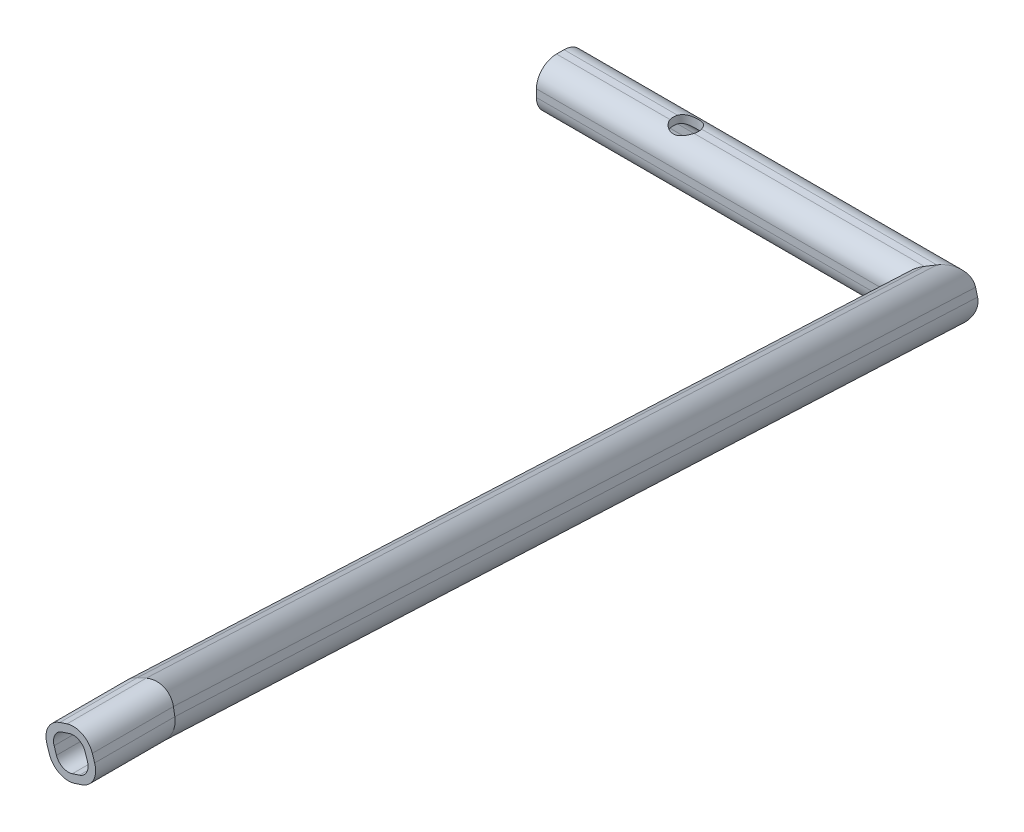
SolidWorks part; units mm, degrees
material "5052-H38, Rod (SS)"
ref_plane "Front Plane" through (0, 0, 0) normal (0, 0, 1) x (1, 0, 0)
ref_plane "Top Plane" through (0, 0, 0) normal (0, 1, 0) x (1, 0, 0)
ref_plane "Right Plane" through (0, 0, 0) normal (1, 0, 0) x (0, 0, -1)
sketch "Sketch2" plane through (0, 0, 0) normal (1, 0, 0) x (0, 0, -1)
  line L1 (-1.5, -6.5) -> (1.5, -6.5)
  line L2 (-6.5, -1.5) -> (-6.5, 1.5)
  line L3 (-1.5, 6.5) -> (1.5, 6.5)
  line L4 (6.5, -1.5) -> (6.5, 1.5)
  line L5 (-6.5, -6.5) -> (6.5, 6.5) construction
  line L6 (-6.5, 6.5) -> (6.5, -6.5) construction
  arc A0 (6.5, -1.5) -> (1.5, -6.5) centre (1.5, -1.5) cw
  arc A1 (-1.5, -6.5) -> (-6.5, -1.5) centre (-1.5, -1.5) cw
  arc A2 (-6.5, 1.5) -> (-1.5, 6.5) centre (-1.5, 1.5) cw
  arc A3 (1.5, 6.5) -> (6.5, 1.5) centre (1.5, 1.5) cw
  point P0 (0, 0)
  dimension "D3" = 5
  dimension "D1" = 13
  dimension "D2" = 13
sketch3d "3DSketch2"
  line L0 (0, 0, 0) -> (335.0752, 0, 0) construction
  line L1 (335.0752, 0, 0) -> (335.0752, 200, 0) construction
  line L2 (335.0752, 200, 0) -> (335.0752, 200, 500) construction
  line L3 (0, 0, 0) -> (150, 0, 0)
  line L4 (150, 0, 0) -> (335.0752, 200, 500)
  line L5 (335.0752, 200, 500) -> (335.0752, 200, 530)
  line L6 (0, 0, 0) -> (0, -210, 0) construction
  dimension "D1" = 150
  dimension "D2" = 30
  dimension "D3" = 200
  dimension "D4" = 500
  dimension "D5" = 210
sweep "Sweep-Thin3" add profiles "Sketch2" path "3DSketch2" parameters "D1"=3
sketch "Sketch21" plane through (0, 0, 0) normal (0, 1, 0) x (1, 0, 0)
  line L0 (0, 0) -> (150, 0) construction
  circle A0 centre (50, 0) radius 5
  dimension "D1" = 10
  dimension "D2" = 50
extrude "Cut-Extrude3" cut sketch "Sketch21" against normal through all both and the other way through all
sketch "Sketch22" [suppressed] plane through (0, 0, 0) normal (0, 0, 1) x (1, 0, 0)
ref_plane "Plane1" [suppressed] through (0, -210, 0) normal (0, 1, 0) x (1, 0, 0)
ref_plane "Plane2" through (0, -210, 0) normal (0, -1, 0) x (-1, 0, 0)
